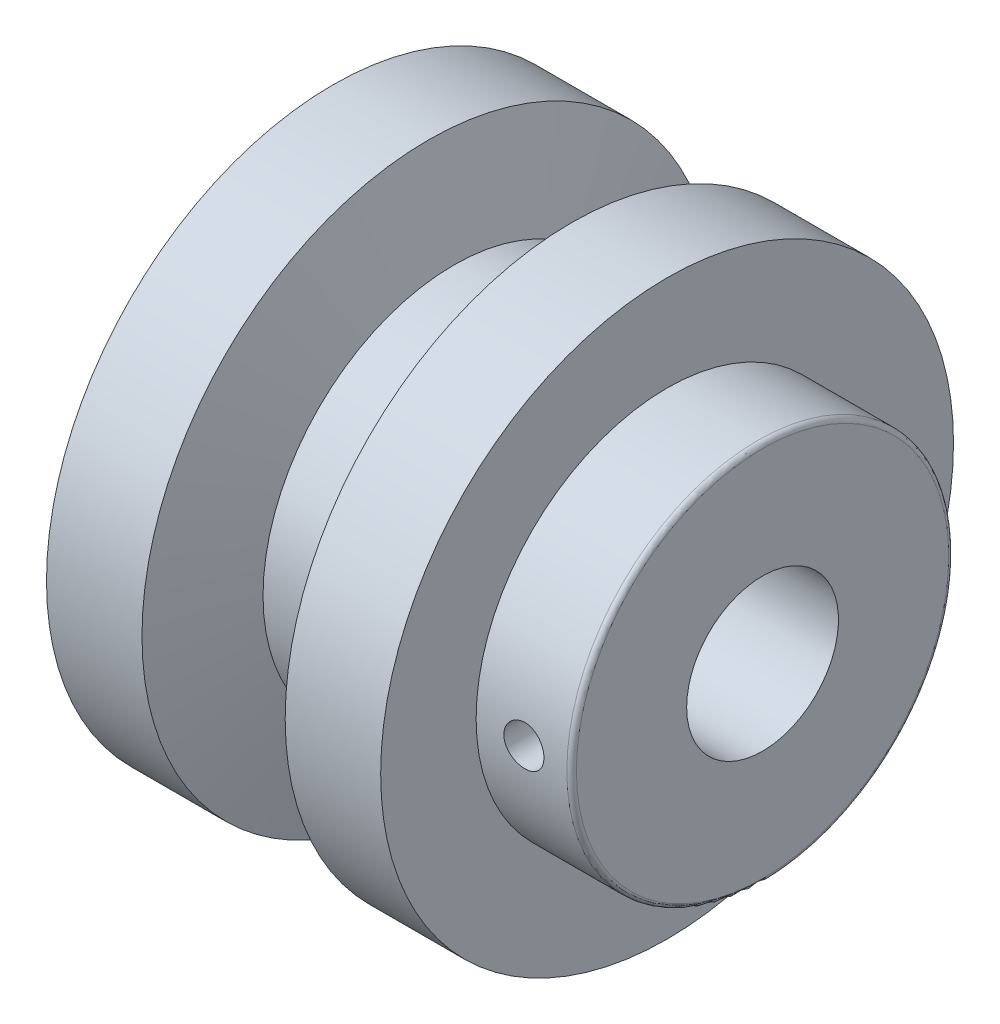
SolidWorks part; units mm, degrees
ref_plane "Front Plane" through (0, 0, 0) normal (0, 0, 1) x (1, 0, 0)
ref_plane "Top Plane" through (0, 0, 0) normal (0, 1, 0) x (1, 0, 0)
ref_plane "Right Plane" through (0, 0, 0) normal (1, 0, 0) x (0, 0, -1)
sketch "Sketch1" plane through (0, 0, 0) normal (0, 0, 1) x (1, 0, 0)
  line L0 (0, 0) -> (43.9763, 0) construction
  line L1 (0, -17.95) -> (0, -30)
  line L3 (10, -30) -> (12.6795, -20)
  line L4 (12.6795, -20) -> (22.3205, -20)
  line L5 (22.3205, -20) -> (25, -30)
  line L6 (25, -30) -> (35, -30)
  line L7 (35, -30) -> (35, -20)
  line L8 (35, -20) -> (44.5, -20)
  line L9 (45, -19.5) -> (45, -7.95)
  line L10 (45, -7.95) -> (2.5, -7.95)
  line L11 (0, -17.95) -> (2.5, -7.95)
  line L12 (10, -30) -> (0, -30)
  arc A0 (44.5, -20) -> (45, -19.5) centre (44.5, -19.5) ccw
  point P18 (35, -30)
  point P21 (25, -30)
  dimension "D11" = 0.5
  dimension "D1" = 15.9
  dimension "D2" = 40
  dimension "D3" = 75
  dimension "D4" = 60
  dimension "D5" = 75
  dimension "D6" = 15
  dimension "D7" = 10
  dimension "D8" = 10
  dimension "D9" = 40
  dimension "D10" = 45
  dimension "D12" = 2.5
  dimension "D13" = 10
revolve "Revolve1" add sketch "Sketch1" angle 360 about L0
hole_wizard "Broca de rosquear para tarraxa de M5x0.81" positions "Esboço2" profile "Esboço1" hole size "M5x0.8" standard "Ansi Metric"
sketch "Esboço2" plane through (0, 0, 0) normal (0, 0, 1) x (1, 0, 0)
  point P0 (40, 0)
sketch "Esboço1" plane through (40, 0, 0) normal (1, 0, 0) x (0, 1, 0)
  line L0 (0, 0) -> (0, 30)
  line L1 (0, 30) -> (2.1, 30)
  line L2 (2.1, 30) -> (2.1, 0)
  line L5 (2.1, 0) -> (0, 0)
  line L11 (0, -6.35) -> (0, 107.95) construction
  dimension "Thru Hole Dia." = 4.2
  dimension "Thru Hole Depth" = 30
cosmetic thread "Representação de rosca1"
